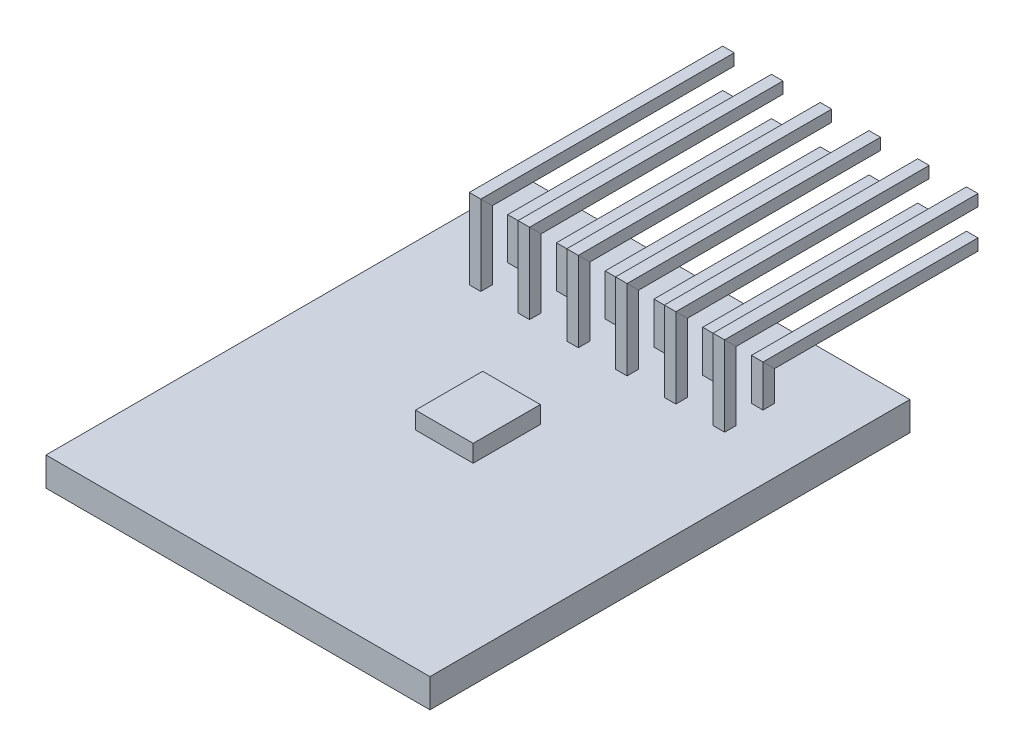
SolidWorks part; units mm, degrees
ref_plane "Front Plane" through (0, 0, 0) normal (0, 0, 1) x (1, 0, 0)
ref_plane "Top Plane" through (0, 0, 0) normal (0, 1, 0) x (1, 0, 0)
ref_plane "Right Plane" through (0, 0, 0) normal (1, 0, 0) x (0, 0, -1)
sketch "Sketch1" plane through (0, 0, 0) normal (0, 1, 0) x (1, 0, 0)
  line L1 (-10, -12.5) -> (10, -12.5)
  line L2 (-10, -12.5) -> (-10, 12.5)
  line L3 (-10, 12.5) -> (10, 12.5)
  line L4 (10, -12.5) -> (10, 12.5)
  line L5 (-10, -12.5) -> (10, 12.5) construction
  line L6 (-10, 12.5) -> (10, -12.5) construction
  point P0 (0, 0)
  dimension "D1" = 20
  dimension "D2" = 25
extrude "Boss-Extrude1" add sketch "Sketch1" along normal blind 1.5
ref_plane "Plane2" through (6.35, 0, 0) normal (1, 0, 0) x (0, 0, -1)
sketch "Sketch2" plane through (6.35, 0, 0) normal (1, 0, 0) x (0, 0, -1)
  line L0 (8.5, -1) -> (8.5, 3.369)
  line L1 (8.5, 3.369) -> (19.5, 3.369)
  line L2 (6.5, -1) -> (6.5, 6.369)
  line L3 (6.5, 6.369) -> (19.5, 6.369)
  line L4 (-12.5, 1.5) -> (12.5, 1.5) construction
  dimension "D1" = 2
  dimension "D2" = 3
  dimension "D3" = 1.869
  dimension "D4" = 1
  dimension "D5" = 4
  dimension "D6" = 13
sketch "Sketch3" plane through (0, 1.5, 0) normal (0, 1, 0) x (1, 0, 0)
  line L0 (6.35, 8.5) -> (6.35, 19.5) construction
  line L1 (6.05, 8.8) -> (6.65, 8.8)
  line L2 (6.05, 8.8) -> (6.05, 8.2)
  line L3 (6.05, 8.2) -> (6.65, 8.2)
  line L4 (6.65, 8.8) -> (6.65, 8.2)
  line L5 (6.05, 8.8) -> (6.65, 8.2) construction
  line L6 (6.05, 8.2) -> (6.65, 8.8) construction
  line L7 (6.35, 6.5) -> (6.35, 19.5) construction
  line L9 (6.05, 6.8) -> (6.65, 6.8)
  line L10 (6.05, 6.8) -> (6.05, 6.2)
  line L11 (6.05, 6.2) -> (6.65, 6.2)
  line L12 (6.65, 6.8) -> (6.65, 6.2)
  line L13 (6.05, 6.8) -> (6.65, 6.2) construction
  line L14 (6.05, 6.2) -> (6.65, 6.8) construction
  point P0 (6.35, 8.5)
  point P9 (6.35, 6.5)
  dimension "D1" = 0.6
sweep "Sweep2" add profiles "Sketch3" path "Sketch2"
chamfer "Chamfer1" distance 0.1 16 edges at (6.35, 5.669, -19.5) (6.05, 5.369, -19.5) (6.35, 5.069, -19.5) (6.65, 5.369, -19.5) (6.35, -1, -6.8) (6.05, -1, -6.5) (6.35, -1, -6.2) (6.65, -1, -6.5) (6.35, -1, -8.8) (6.05, -1, -8.5) (6.35, -1, -8.2) (6.65, -1, -8.5) (6.35, 3.669, -19.5) (6.05, 3.369, -19.5) (6.35, 3.069, -19.5) (6.65, 3.369, -19.5)
pattern_linear "LPattern3" count 6 spacing 2.54 along (-1, 0, 0) of "Sweep2", "Chamfer1"
sketch "Sketch4" plane through (0, 1.5, 0) normal (0, 1, 0) x (1, 0, 0)
  line L1 (-1.5, -1.75) -> (1.5, -1.75)
  line L2 (-1.5, -1.75) -> (-1.5, 1.75)
  line L3 (-1.5, 1.75) -> (1.5, 1.75)
  line L4 (1.5, -1.75) -> (1.5, 1.75)
  line L5 (-1.5, -1.75) -> (1.5, 1.75) construction
  line L6 (-1.5, 1.75) -> (1.5, -1.75) construction
  point P0 (0, 0)
  dimension "D1" = 3
  dimension "D2" = 3.5
extrude "Boss-Extrude2" add sketch "Sketch4" along normal blind 0.9
sketch "Sketch5" plane through (0, 1.5, 0) normal (0, 1, 0) x (1, 0, 0)
  line L0 (0, -5.825) -> (0, -9.1652)
  line L1 (0, -5.825) -> (-3.3401, -5.825)
  line L2 (0, -5.825) -> (0.9535, -6.3008)
  text T0 "X" font "Century Gothic" height in points 3
  text T1 "Y" font "Century Gothic" height in points 3
  text T2 "Z" font "Century Gothic" height in points 3
